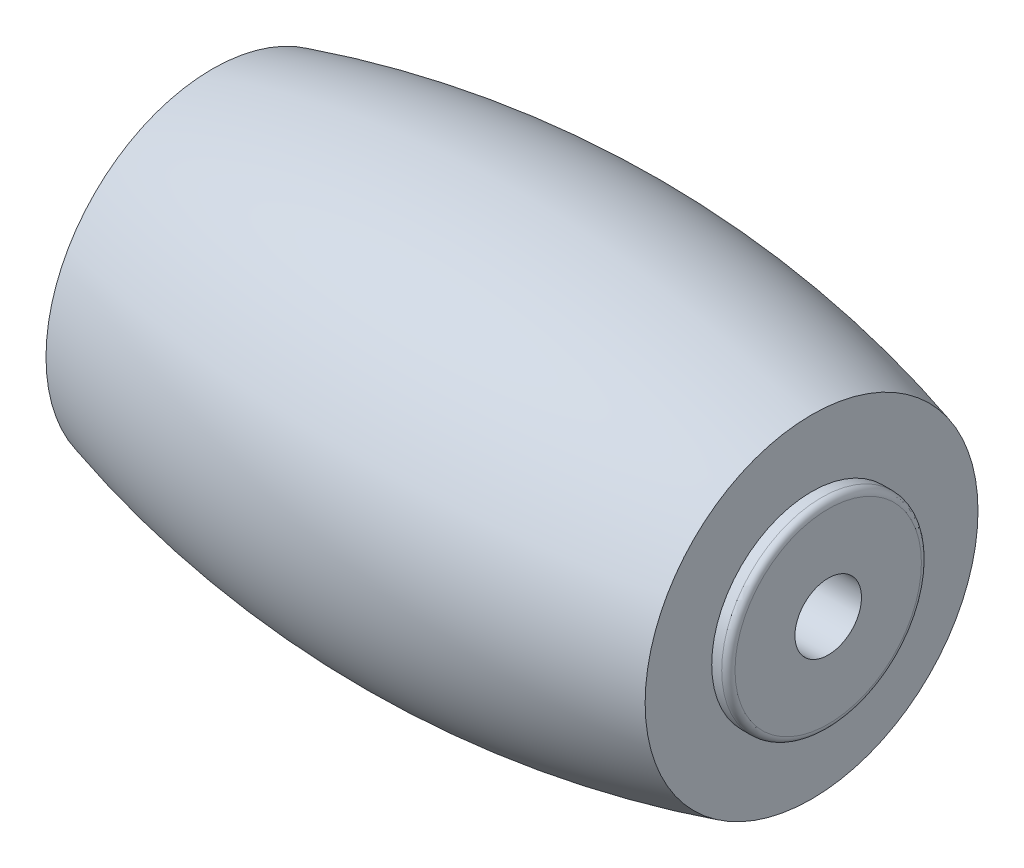
SolidWorks part; units mm, degrees
ref_plane "Front Plane" through (0, 0, 0) normal (0, 0, 1) x (1, 0, 0)
ref_plane "Top Plane" through (0, 0, 0) normal (0, 1, 0) x (1, 0, 0)
ref_plane "Right Plane" through (0, 0, 0) normal (1, 0, 0) x (0, 0, -1)
sketch "Sketch1" plane through (0, 0, 0) normal (0, 1, 0) x (1, 0, 0)
  line L0 (0, 0) -> (-202751.7478, 0) construction
  line L1 (0, 0) -> (0, -202751.7478) construction
  line L2 (0, 0) -> (-9, 0)
  line L3 (-9, 0) -> (-9, 5)
  line L4 (0, 0) -> (9, 0)
  line L5 (9, 0) -> (9, 5)
  arc A0 (-9, 5) -> (9, 5) centre (0, -26.7836) cw
  dimension "D1" = 9
  dimension "D2" = 5
revolve "Revolve1" add sketch "Sketch1" angle 360 about L0
sketch "Sketch3" plane through (9, 0, 0) normal (1, 0, 0) x (0, 0, -1)
  circle A0 centre (0, 0) radius 3
  dimension "D1" = 6
extrude "Boss-Extrude1" add sketch "Sketch3" along normal blind 0.5
ref_plane "Plane1" through (0, 0, 0) normal (1, 0, 0) x (0, 0, -1)
mirror "Mirror1" about plane through (0, 0, 0) normal (1, 0, 0) of "Boss-Extrude1"
sketch "Sketch4" plane through (-9.5, 0, 0) normal (-1, 0, 0) x (0, 0, 1)
  circle A0 centre (0, 0) radius 1
  dimension "D1" = 2
extrude "Cut-Extrude2" cut sketch "Sketch4" against normal through all
fillet "Fillet1" radius 0.2 2 edges at (9.5, 0, -3) (-9.5, 0, -3)
scale "ｽｹｰﾙ1" scale about centroid uniform scaling yes scale factor 0.894737
